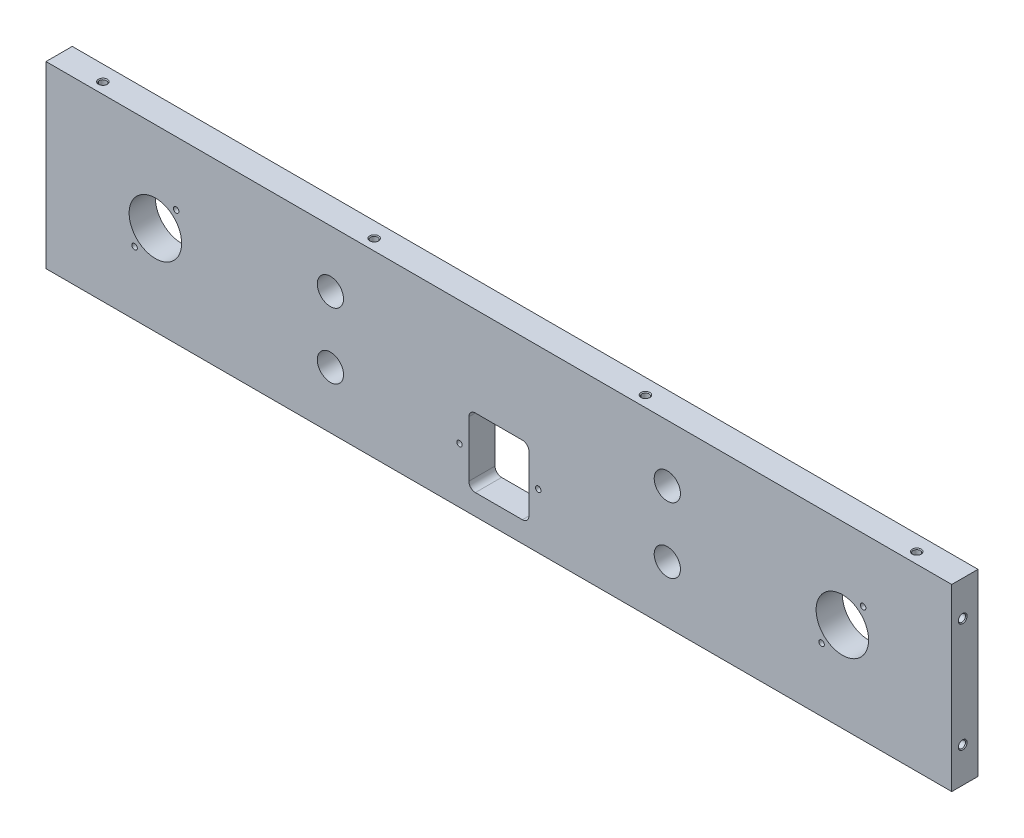
SolidWorks part; units mm, degrees
material "3.3523 (EN-AW 5052)"
ref_plane "前基準面" through (0, 0, 0) normal (0, 0, 1) x (1, 0, 0)
ref_plane "上基準面" through (0, 0, 0) normal (0, 1, 0) x (1, 0, 0)
ref_plane "右基準面" through (0, 0, 0) normal (1, 0, 0) x (0, 0, -1)
sketch "草圖1" plane through (0, 0, 0) normal (0, 0, 1) x (1, 0, 0)
  line L1 (0, 0) -> (414, 0)
  line L2 (0, 0) -> (0, 82)
  line L3 (0, 82) -> (414, 82)
  line L4 (414, 0) -> (414, 82)
  dimension "D1" = 82
  dimension "D2" = 414
extrude "填料-伸長1" add sketch "草圖1" along normal blind 12
sketch "草圖2" plane through (0, 0, 0) normal (0, 0, 1) x (1, 0, 0)
  line L0 (0, 82) -> (0, 0) construction
  line L1 (193.25, 9.5) -> (220.75, 9.5)
  line L2 (193.25, 9.5) -> (193.25, 41)
  line L3 (193.25, 41) -> (220.75, 41)
  line L4 (220.75, 9.5) -> (220.75, 41)
  line L5 (193.25, 9.5) -> (220.75, 41) construction
  line L6 (193.25, 41) -> (220.75, 9.5) construction
  line L7 (414, 0) -> (414, 82) construction
  line L8 (414, 82) -> (0, 82) construction
  line L9 (0, 41) -> (414, 41) construction
  circle A0 centre (130, 56) radius 6
  circle A1 centre (130, 26) radius 6
  circle A2 centre (284, 56) radius 6
  circle A3 centre (284, 26) radius 6
  circle A4 centre (50, 41) radius 12
  circle A5 centre (364, 41) radius 12
  point P0 (207, 25.25)
  dimension "D1" = 24
  dimension "D2" = 24
  dimension "D3" = 12
  dimension "D4" = 12
  dimension "D5" = 12
  dimension "D6" = 12
  dimension "D7" = 130
  dimension "D8" = 50
  dimension "D9" = 50
  dimension "D10" = 207
  dimension "D11" = 130
  dimension "D12" = 41
  dimension "D13" = 41
  dimension "D14" = 30
  dimension "D15" = 30
  dimension "D16" = 15
  dimension "D17" = 15
  dimension "D18" = 27.5
  dimension "D19" = 31.5
extrude "除料-伸長5" cut sketch "草圖2" along normal through all
fillet "圓角1" radius 3 4 edges at (193.25, 9.5, 6) (220.75, 9.5, 6) (220.75, 41, 6) (193.25, 41, 6)
hole_wizard "M3 螺紋孔1" positions "草圖3" profile "草圖4" tap size "M3" standard "ISO" end condition through all
sketch "草圖3" plane through (0, 0, 0) normal (0, 0, 1) x (1, 0, 0)
  line L1 (217.75, 41) -> (196.25, 41) construction
  line L5 (196.25, 9.5) -> (217.75, 9.5) construction
  circle A0 centre (50, 41) radius 12 construction
  circle A1 centre (364, 41) radius 12 construction
  point P0 (59.5, 53)
  point P2 (40.5, 29)
  point P4 (189, 25.25)
  point P6 (225, 25.25)
  point P8 (373.5, 53)
  point P10 (354.5, 29)
  point P24 (207, 41)
  dimension "D1" = 19
  dimension "D2" = 24
  dimension "D3" = 12
  dimension "D4" = 9.5
  dimension "D5" = 36
  dimension "D6" = 18
  dimension "D7" = 15.75
  dimension "D8" = 19
  dimension "D9" = 9.5
  dimension "D10" = 24
  dimension "D11" = 12
sketch "草圖4" plane through (59.5, 53, 0) normal (1, 0, 0) x (0, 1, 0)
  line L0 (0, 0) -> (0, 12)
  line L1 (0, 12) -> (1.25, 12)
  line L2 (1.25, 12) -> (1.25, 0.275)
  line L3 (1.25, 0.275) -> (1.525, 0)
  line L5 (1.525, 0) -> (0, 0)
  line L6 (-1.25, 0.275) -> (-1.525, 0) construction
  line L11 (0, -6.35) -> (0, 107.95) construction
  dimension "貫穿螺孔鑽直徑" = 2.5
  dimension "貫穿螺孔鑽深度" = 12
  dimension "近端錐孔直徑" = 3.05
  dimension "近端錐孔角度" = 90
cosmetic thread "鑽孔螺紋19" parameters "D2"=3
cosmetic thread "鑽孔螺紋20" parameters "D2"=3
cosmetic thread "鑽孔螺紋21" parameters "D2"=3
cosmetic thread "鑽孔螺紋22" parameters "D2"=3
cosmetic thread "鑽孔螺紋23" parameters "D2"=3
cosmetic thread "鑽孔螺紋24" parameters "D2"=3
hole_wizard "M4 螺紋孔1" positions "草圖5" profile "草圖6" tap size "M4" standard "ISO" end condition through all
sketch "草圖5" plane through (0, 82, 0) normal (0, 1, 0) x (1, 0, 0)
  line L1 (0, -6) -> (414, -6) construction
  line L2 (0, -12) -> (0, 0) construction
  line L3 (414, -12) -> (414, 0) construction
  point P0 (21, -7)
  point P2 (145, -7)
  point P4 (269, -7)
  point P6 (393, -7)
  dimension "D1" = 1
  dimension "D2" = 21
  dimension "D3" = 124
  dimension "D4" = 124
  dimension "D5" = 124
cosmetic thread "鑽孔螺紋7" parameters "D2"=4
cosmetic thread "鑽孔螺紋8" parameters "D2"=4
cosmetic thread "鑽孔螺紋9" parameters "D2"=4
cosmetic thread "鑽孔螺紋10" parameters "D2"=4
sketch "草圖6" plane through (21, 82, 7) normal (1, 0, 0) x (0, 0, 1)
  line L0 (0, 0) -> (0, 82)
  line L1 (0, 82) -> (1.65, 82)
  line L2 (1.65, 82) -> (1.65, 0.375)
  line L3 (1.65, 0.375) -> (2.025, 0)
  line L5 (2.025, 0) -> (0, 0)
  line L6 (-1.65, 0.375) -> (-2.025, 0) construction
  line L11 (0, -6.35) -> (0, 107.95) construction
  dimension "貫穿螺孔鑽直徑" = 3.3
  dimension "貫穿螺孔鑽深度" = 82
  dimension "近端錐孔直徑" = 4.05
  dimension "近端錐孔角度" = 90
hole_wizard "M4 螺紋孔3" positions "草圖9" profile "草圖10" tap size "M4" standard "ISO"
sketch "草圖9" plane through (414, 0, 0) normal (1, 0, 0) x (0, 0, -1)
  line L1 (-6, 0) -> (-6, 82) construction
  line L2 (-12, 0) -> (0, 0) construction
  line L3 (-12, 82) -> (0, 82) construction
  point P0 (-7, 16)
  point P2 (-7, 66)
  dimension "D1" = 50
  dimension "D2" = 16
  dimension "D3" = 1
sketch "草圖10" plane through (414, 16, 7) normal (0, 1, 0) x (0, 0, -1)
  line L0 (0, 0) -> (0, 8.0914)
  line L1 (0, 8.0914) -> (1.65, 7.1)
  line L2 (1.65, 7.1) -> (1.65, 0.375)
  line L3 (1.65, 0.375) -> (2.025, 0)
  line L5 (2.025, 0) -> (0, 0)
  line L6 (-1.65, 0.375) -> (-2.025, 0) construction
  line L10 (0, 8.0914) -> (-1.65, 7.1) construction
  line L11 (0, -6.35) -> (0, 107.95) construction
  dimension "螺孔鑽直徑" = 3.3
  dimension "螺孔鑽深度" = 7.1
  dimension "近端錐孔直徑" = 4.05
  dimension "近端錐孔角度" = 90
  dimension "導頭角度" = 118
cosmetic thread "鑽孔螺紋15" parameters "D1"=5, "D2"=4
cosmetic thread "鑽孔螺紋16" parameters "D1"=5, "D2"=4
hole_wizard "M4 螺紋孔4" positions "草圖11" profile "草圖12" tap size "M4" standard "ISO"
sketch "草圖11" plane through (0, 0, 0) normal (-1, 0, 0) x (0, 0, 1)
  line L0 (6, 0) -> (6, 82) construction
  line L1 (12, 0) -> (0, 0) construction
  line L2 (12, 82) -> (0, 82) construction
  point P0 (7, 16)
  point P2 (7, 66)
  dimension "D1" = 1
  dimension "D2" = 16
  dimension "D3" = 50
cosmetic thread "鑽孔螺紋17" parameters "D1"=5, "D2"=4
cosmetic thread "鑽孔螺紋18" parameters "D1"=5, "D2"=4
sketch "草圖12" plane through (0, 16, 7) normal (0, 1, 0) x (0, 0, 1)
  line L0 (0, 0) -> (0, 8.0914)
  line L1 (0, 8.0914) -> (1.65, 7.1)
  line L2 (1.65, 7.1) -> (1.65, 0.375)
  line L3 (1.65, 0.375) -> (2.025, 0)
  line L5 (2.025, 0) -> (0, 0)
  line L6 (-1.65, 0.375) -> (-2.025, 0) construction
  line L10 (0, 8.0914) -> (-1.65, 7.1) construction
  line L11 (0, -6.35) -> (0, 107.95) construction
  dimension "螺孔鑽直徑" = 3.3
  dimension "螺孔鑽深度" = 7.1
  dimension "近端錐孔直徑" = 4.05
  dimension "近端錐孔角度" = 90
  dimension "導頭角度" = 118
